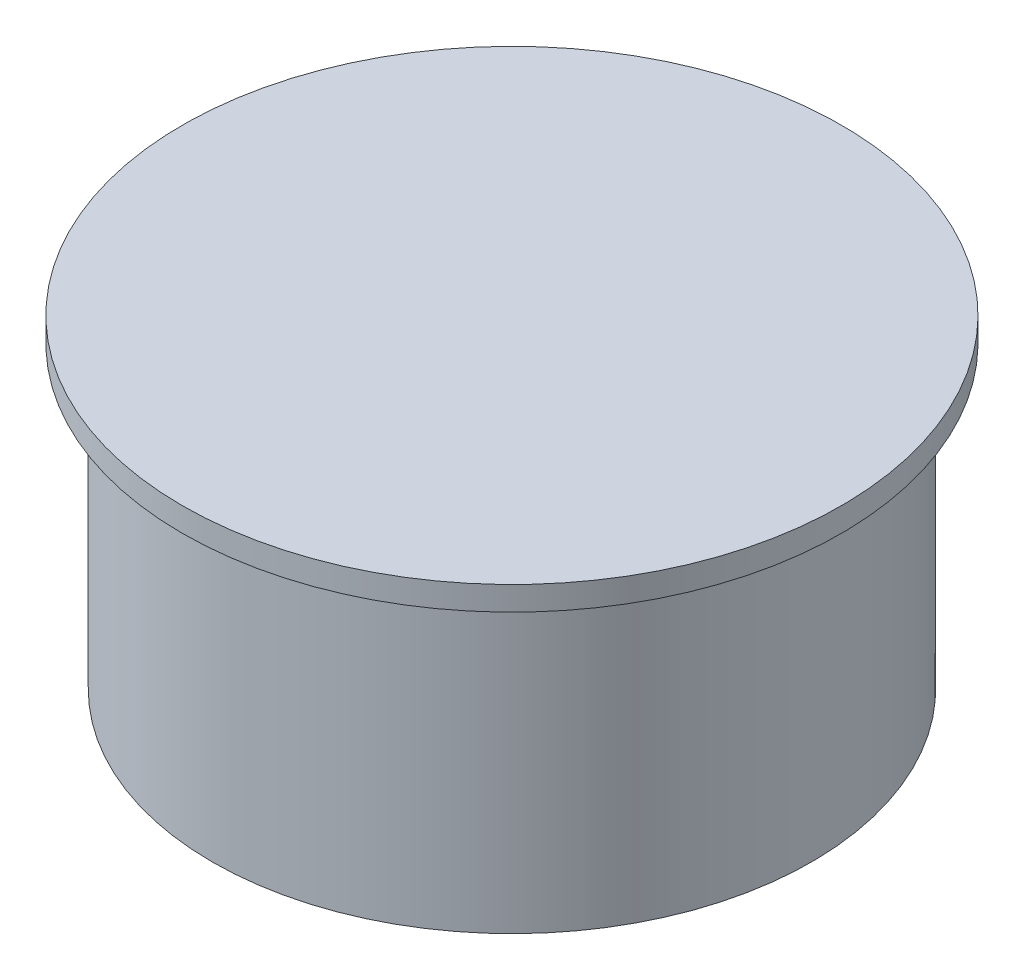
SolidWorks part; units mm, degrees
ref_plane "Front Plane" through (0, 0, 0) normal (0, 0, 1) x (1, 0, 0)
ref_plane "Top Plane" through (0, 0, 0) normal (0, 1, 0) x (1, 0, 0)
ref_plane "Right Plane" through (0, 0, 0) normal (1, 0, 0) x (0, 0, -1)
sketch "Sketch1" plane through (0, 0, 0) normal (0, 1, 0) x (1, 0, 0)
  circle A0 centre (0, 0) radius 5
extrude "Boss-Extrude1" add sketch "Sketch1" along normal blind 5
sketch "Sketch2" plane through (0, 5, 0) normal (0, 1, 0) x (1, 0, 0)
  circle A0 centre (0, 0) radius 5.5
extrude "Boss-Extrude2" add sketch "Sketch2" along normal blind 0.4
